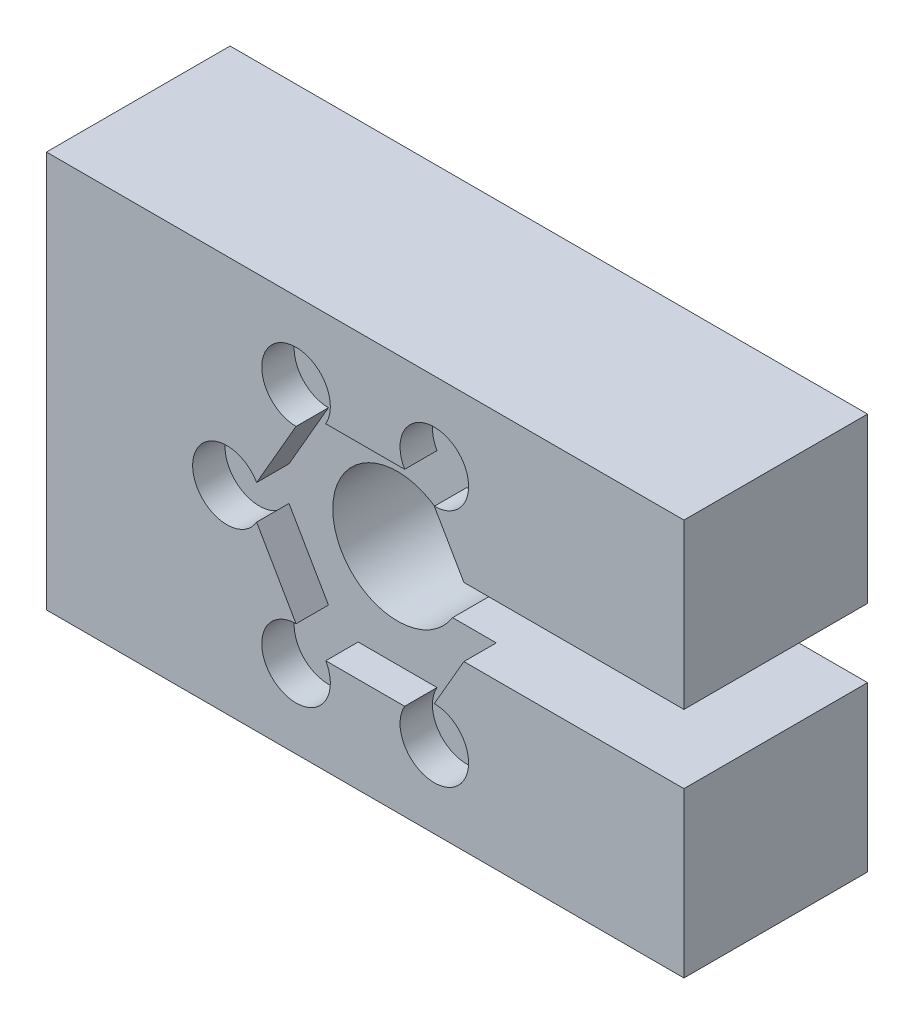
SolidWorks part; units mm, degrees
ref_plane "Front Plane" through (0, 0, 0) normal (0, 0, 1) x (1, 0, 0)
ref_plane "Top Plane" through (0, 0, 0) normal (0, 1, 0) x (1, 0, 0)
ref_plane "Right Plane" through (0, 0, 0) normal (1, 0, 0) x (0, 0, -1)
sketch "Sketch1" plane through (0, 0, 0) normal (0, 0, 1) x (1, 0, 0)
  line L0 (-5.4848, 0) -> (14.7554, 0) construction
  line L1 (-2.7424, 4.75) -> (-5.4848, 0)
  line L2 (-5.4848, 0) -> (-2.7424, -4.75)
  line L3 (-2.7424, -4.75) -> (2.7424, -4.75)
  line L4 (2.7424, -4.75) -> (4.5683, -1.5875)
  line L5 (4.5683, 1.5875) -> (2.7424, 4.75)
  line L6 (2.7424, 4.75) -> (-2.7424, 4.75)
  line L7 (-14.7554, -9.179) -> (14.7554, -9.179)
  line L8 (-14.7554, -9.179) -> (-14.7554, 9.179)
  line L9 (-14.7554, 9.179) -> (14.7554, 9.179)
  line L10 (14.7554, -9.179) -> (14.7554, -1.5875)
  line L11 (-14.7554, -9.179) -> (14.7554, 9.179) construction
  line L12 (-14.7554, 9.179) -> (14.7554, -9.179) construction
  line L13 (14.7554, -1.5875) -> (4.5683, -1.5875)
  line L15 (14.7554, 1.5875) -> (4.5683, 1.5875)
  line L17 (14.7554, 1.5875) -> (14.7554, 9.179)
  circle A0 centre (0, 0) radius 4.75 construction
  dimension "D1" = 9.5
  dimension "D2" = 3.175
extrude "Boss-Extrude1" add sketch "Sketch1" along normal blind 1.5
sketch "Sketch4" plane through (0, 0, 0) normal (0, 0, -1) x (-1, 0, 0)
  line L1 (-4.5683, 1.5875) -> (-2.5456, 1.5875)
  line L2 (-4.5683, -1.5875) -> (-2.5456, -1.5875)
  line L13 (-14.7554, 9.179) -> (-14.7554, 1.5875)
  line L14 (-14.7554, 1.5875) -> (-4.5683, 1.5875)
  line L15 (-4.5683, 1.5875) -> (-2.7424, 4.75)
  line L16 (-2.7424, 4.75) -> (2.7424, 4.75)
  line L17 (2.7424, 4.75) -> (5.4848, 0)
  line L18 (5.4848, 0) -> (2.7424, -4.75)
  line L19 (2.7424, -4.75) -> (-2.7424, -4.75)
  line L20 (-2.7424, -4.75) -> (-4.5683, -1.5875)
  line L21 (-4.5683, -1.5875) -> (-14.7554, -1.5875)
  line L22 (-14.7554, -1.5875) -> (-14.7554, -9.179)
  line L23 (-14.7554, -9.179) -> (14.7554, -9.179)
  line L24 (14.7554, -9.179) -> (14.7554, 9.179)
  line L25 (14.7554, 9.179) -> (-14.7554, 9.179)
  line L26 (-14.7554, 9.179) -> (-14.7554, 1.5875)
  line L27 (-14.7554, 1.5875) -> (-4.5683, 1.5875)
  line L34 (-4.5683, -1.5875) -> (-14.7554, -1.5875)
  line L35 (-14.7554, -1.5875) -> (-14.7554, -9.179)
  line L36 (-14.7554, -9.179) -> (14.7554, -9.179)
  line L37 (14.7554, -9.179) -> (14.7554, 9.179)
  line L38 (14.7554, 9.179) -> (-14.7554, 9.179)
  arc A0 (-2.5456, -1.5875) -> (-2.5456, 1.5875) centre (0, 0) ccw
  dimension "D2" = 6
  dimension "D1" = 0
extrude "Boss-Extrude2" add sketch "Sketch4" along normal blind 7
sketch "Sketch5" plane through (0, 0, 1.5) normal (0, 0, 1) x (1, 0, 0)
  line L0 (-2.7424, 4.75) -> (2.7424, 4.75) construction
  line L1 (2.7424, 4.75) -> (4.5683, 1.5875) construction
  line L2 (2.7424, 4.75) -> (4.5683, 1.5875) construction
  circle A0 centre (1.8259, 3.1625) radius 1.5875 construction
  circle A1 centre (3.2007, 5.5438) radius 1.5875
  circle A2 centre (6.4014, 0) radius 1.5875
  circle A3 centre (3.2007, -5.5438) radius 1.5875
  circle A4 centre (-3.2007, -5.5437) radius 1.5875
  circle A5 centre (-6.4014, 0) radius 1.5875
  circle A6 centre (-3.2007, 5.5438) radius 1.5875
  point P8 (1.8259, 4.75)
  point P9 (3.2007, 3.9563)
  point P25 (0, 0)
  dimension "D1" = 3.175
  dimension "D2" = 3.175
  dimension "D3" = 6
extrude "Cut-Extrude1" cut sketch "Sketch5" against normal up to surface (1.5 mm away) up to face at (0.3553, 0, 0)
